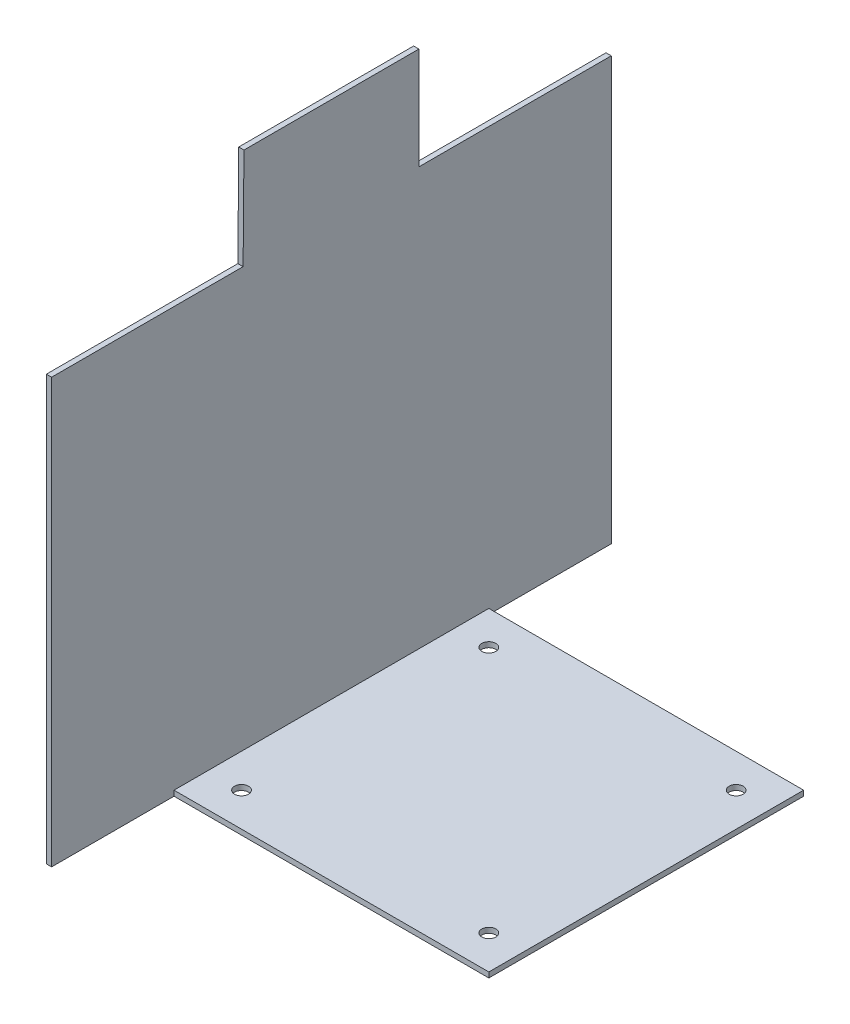
SolidWorks part; units mm, degrees
ref_plane "Front Plane" through (0, 0, 0) normal (0, 0, 1) x (1, 0, 0)
ref_plane "Top Plane" through (0, 0, 0) normal (0, 1, 0) x (1, 0, 0)
ref_plane "Right Plane" through (0, 0, 0) normal (1, 0, 0) x (0, 0, -1)
sketch "Sketch1" plane through (0, 0, 0) normal (1, 0, 0) x (0, 0, -1)
  line L1 (-160, -150) -> (160, -150)
  line L2 (-160, -150) -> (-160, 150)
  line L3 (-160, 150) -> (160, 150)
  line L4 (160, -150) -> (160, 150)
  line L5 (-160, -150) -> (160, 150) construction
  line L6 (-160, 150) -> (160, -150) construction
  point P0 (0, 0)
  dimension "D1" = 320
  dimension "D2" = 300
extrude "Boss-Extrude1" add sketch "Sketch1" along normal blind 3
sketch "Sketch2" plane through (0, -150, 0) normal (0, -1, 0) x (1, 0, 0)
  line L0 (3, 90) -> (183, 90)
  line L1 (3, 160) -> (3, -160) construction
  line L2 (183, 90) -> (183, -90)
  line L3 (183, -90) -> (3, -90)
  line L4 (3, -90) -> (3, 90)
  line L5 (3, 160) -> (0, 160) construction
  line L6 (3, -160) -> (0, -160) construction
  circle A0 centre (22.29, -70.71) radius 4
  circle A1 centre (22.29, 70.71) radius 4
  circle A2 centre (163.71, 70.71) radius 4
  circle A3 centre (163.71, -70.71) radius 4
  dimension "D4" = 8
  dimension "D5" = 8
  dimension "D6" = 8
  dimension "D7" = 8
  dimension "D1" = 70
  dimension "D2" = 70
  dimension "D3" = 180
  dimension "D8" = 19.29
  dimension "D9" = 141.42
  dimension "D10" = 19.29
  dimension "D11" = 141.42
  dimension "D12" = 141.42
  dimension "D13" = 19.29
extrude "Boss-Extrude2" add sketch "Sketch2" against normal blind 3
sketch "Sketch3" plane through (3, 0, 0) normal (1, 0, 0) x (0, 0, -1)
  line L0 (-50, 152) -> (-50.5, 92.5)
  line L4 (-174.9953, 153.8498) -> (-150, 158.8997)
  line L5 (-150, 158.8997) -> (-50, 152)
  line L6 (186.0168, 162.2069) -> (50, 152)
  line L7 (50, 152) -> (50, 91.6555)
  line L8 (50, -823) -> (50, 137) construction
  line L12 (186.0168, 91.6555) -> (186.0168, 162.2069)
  line L15 (50, 91.6555) -> (186.0168, 91.6555)
  line L16 (-50.5, 92.5) -> (-174.9953, 92.5)
  line L17 (-174.9953, 92.5) -> (-174.9953, 153.8498)
extrude "Cut-Extrude1" cut sketch "Sketch3" against normal blind 10
